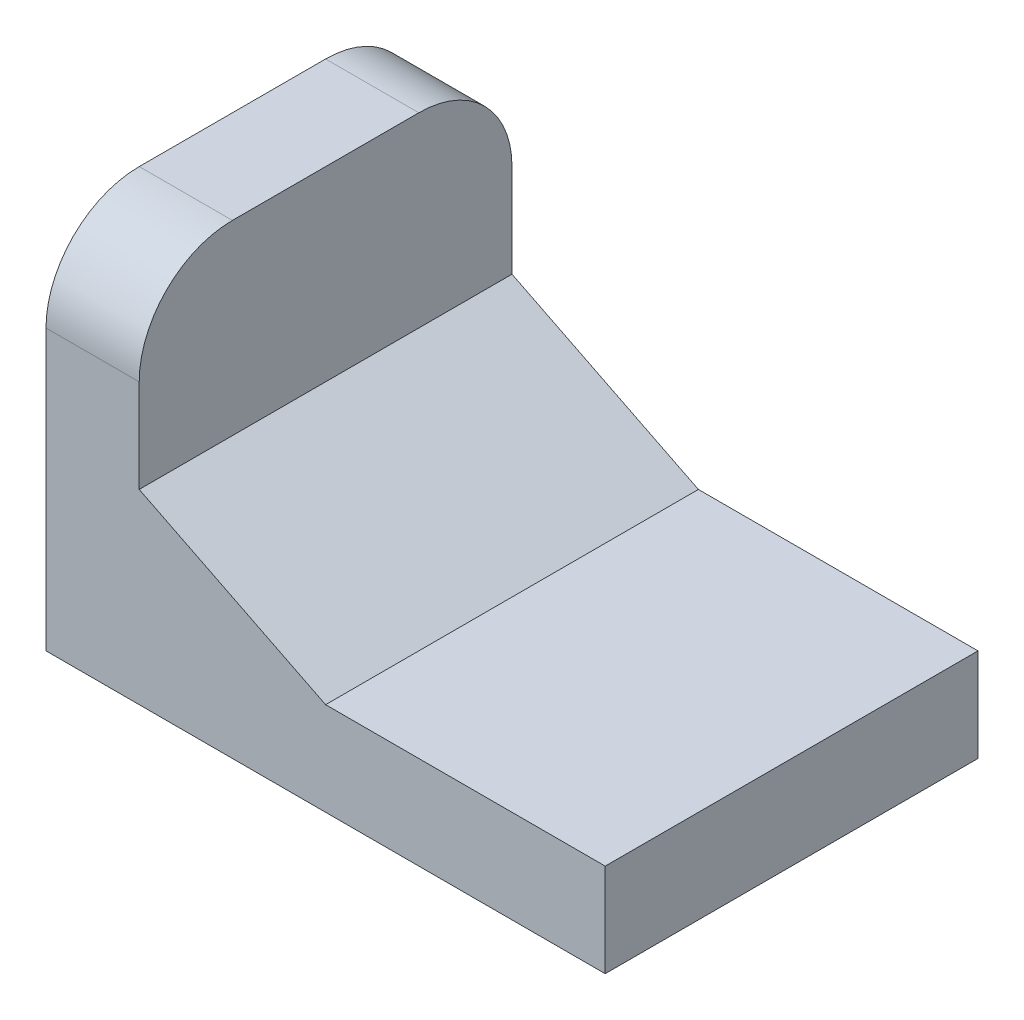
SolidWorks part; units mm, degrees
ref_plane "前基準面" through (0, 0, 0) normal (0, 0, 1) x (1, 0, 0)
ref_plane "上基準面" through (0, 0, 0) normal (0, 1, 0) x (1, 0, 0)
ref_plane "右基準面" through (0, 0, 0) normal (1, 0, 0) x (0, 0, -1)
sketch "草圖1" plane through (0, 0, 0) normal (0, 0, 1) x (1, 0, 0)
  line L0 (15, 5) -> (5, 10)
  line L1 (0, 0) -> (5, 0)
  line L2 (0, 0) -> (0, 20)
  line L3 (0, 20) -> (5, 20)
  line L4 (5, 10) -> (5, 20)
  line L5 (0, 0) -> (30, 0)
  line L6 (0, 0) -> (0, 5)
  line L7 (15, 5) -> (30, 5)
  line L8 (30, 0) -> (30, 5)
  point P10 (2.5, 20)
  dimension "D1" = 30
  dimension "D2" = 5
  dimension "D3" = 15
  dimension "D4" = 20
  dimension "D5" = 5
  dimension "D6" = 10
extrude "填料-伸長1" add sketch "草圖1" along normal blind 20 contours L5 L8 L7 L0 L4 L3 L2 L1
fillet "圓角1" radius 5 2 edges at (2.5, 20, 0) (2.5, 20, 20)
scale "縮放比例1" scale about centroid uniform scaling yes scale factor 0.2
